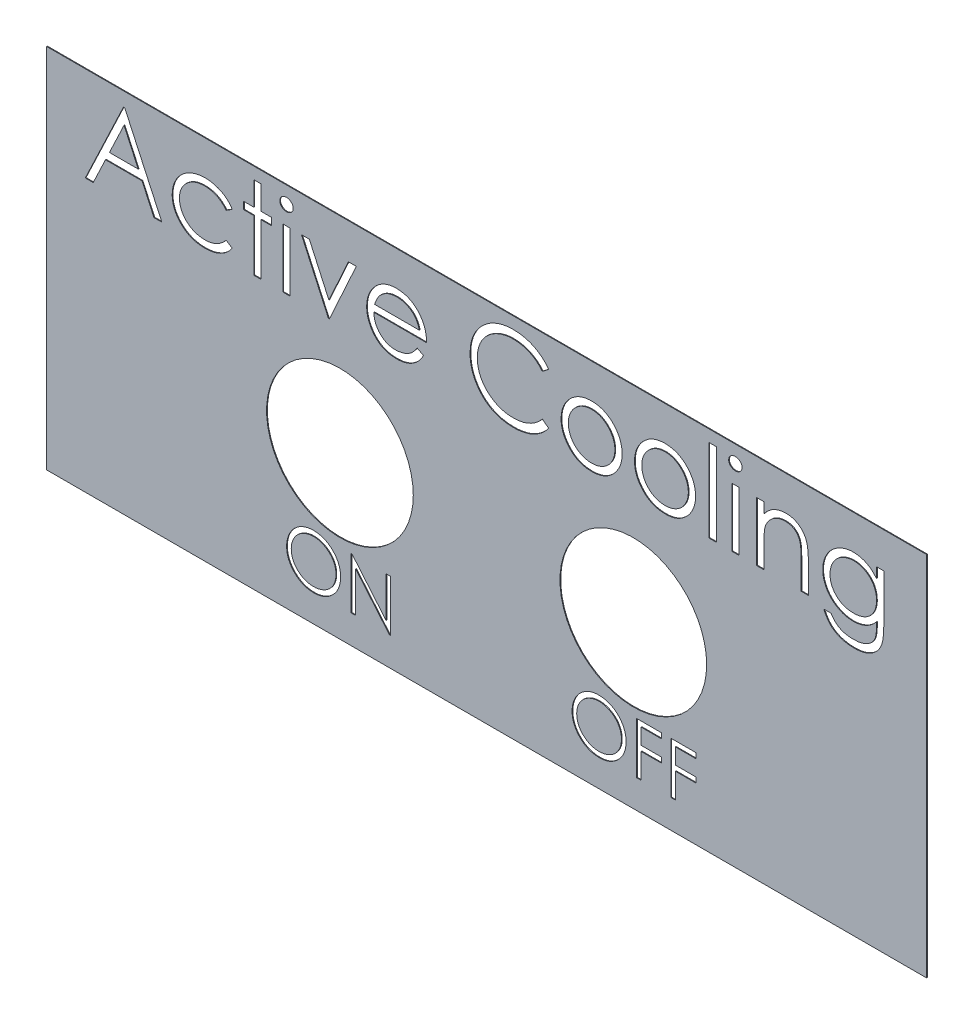
SolidWorks part; units mm, degrees
ref_plane "Front Plane" through (0, 0, 0) normal (0, 0, 1) x (1, 0, 0)
ref_plane "Top Plane" through (0, 0, 0) normal (0, 1, 0) x (1, 0, 0)
ref_plane "Right Plane" through (0, 0, 0) normal (1, 0, 0) x (0, 0, -1)
sketch "Sketch1" plane through (0, 0, 0) normal (0, 0, 1) x (1, 0, 0)
  line L0 (0, 17.5) -> (60, 17.5) construction
  line L1 (0, 0) -> (60, 0)
  line L2 (0, 0) -> (0, 25)
  line L3 (0, 25) -> (60, 25)
  line L4 (60, 0) -> (60, 25)
  line L5 (0, 11) -> (60, 11) construction
  line L6 (20, 0) -> (20, 25) construction
  line L7 (40, 0) -> (40, 25) construction
  line L8 (15, 2) -> (25, 2) construction
  line L9 (25, 0) -> (25, 25) construction
  line L10 (15, 0) -> (15, 25) construction
  line L11 (45, 0) -> (45, 25) construction
  line L12 (35, 0) -> (35, 25) construction
  line L13 (35, 2) -> (45, 2) construction
  circle A0 centre (20, 11) radius 5
  circle A1 centre (40, 11) radius 5
  text T0 "Cooling System" font "Century Gothic" height 5
  text T1 "ON" font "Century Gothic" height 3
  text T2 "OFF" font "Century Gothic" height 3
  dimension "D7" = 10
  dimension "D8" = 10
  dimension "D1" = 25
  dimension "D2" = 60
  dimension "D3" = 7.5
  dimension "D4" = 11
  dimension "D5" = 20
  dimension "D9" = 2
  dimension "D6" = 2
  dimension "D10" = 2
  dimension "D11" = 2
  dimension "D12" = 2
  dimension "D13" = 2
extrude "Boss-Extrude1" add sketch "Sketch1" along normal blind 0.05 contours L1 L4 L3 L2 A1 A0
sketch "Sketch2" plane through (0, 0, 0.05) normal (0, 0, 1) x (1, 0, 0)
  line L0 (15, 11) -> (15, 1.9383) construction
  line L1 (15, 1.9383) -> (25, 1.9383) construction
  line L2 (25, 1.9383) -> (25, 11) construction
  line L3 (35, 11) -> (35, 1.9383) construction
  line L4 (35, 1.9383) -> (45, 1.9383) construction
  line L5 (45, 1.9383) -> (45, 11) construction
  line L6 (0, 18.5545) -> (60, 18.5545) construction
  line L7 (0, 0) -> (0, 25) construction
  line L8 (60, 0) -> (60, 25) construction
  circle A0 centre (20, 11) radius 5 construction
  circle A1 centre (40, 11) radius 5 construction
  text T0 "ON"
  text T1 "OFF"
  text T2 "Active Cooling" font "Century Gothic" height 5.5
extrude "Cut-Extrude1" cut sketch "Sketch2" against normal through all
